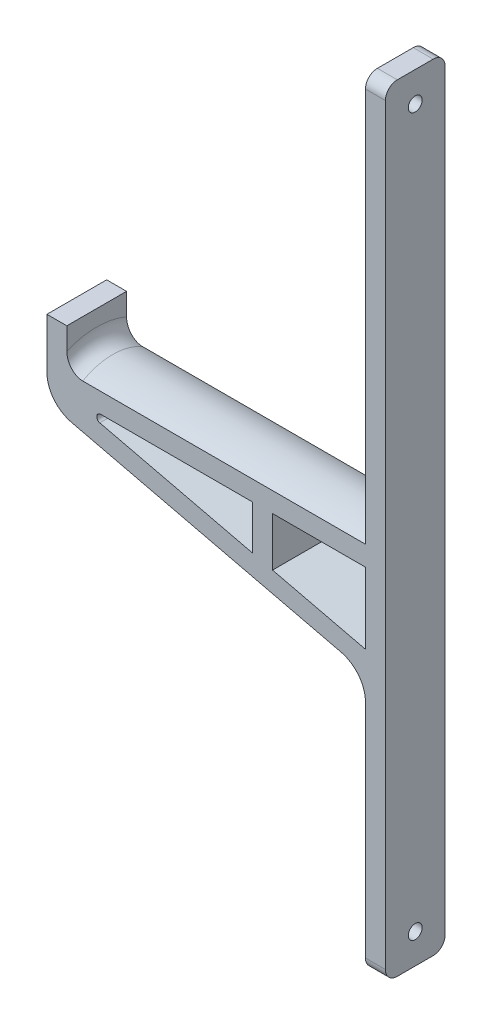
SolidWorks part; units mm, degrees
ref_plane "Plano frontal" through (0, 0, 0) normal (0, 0, 1) x (1, 0, 0)
ref_plane "Plano superior" through (0, 0, 0) normal (0, 1, 0) x (1, 0, 0)
ref_plane "Plano direito" through (0, 0, 0) normal (1, 0, 0) x (0, 0, -1)
sketch "Esboço1" plane through (0, 0, 0) normal (0, 0, 1) x (1, 0, 0)
  line L0 (-2.5, -2.5) -> (-77.5, -2.5)
  line L1 (2.5, 97.5) -> (-2.5, 97.5)
  line L2 (2.5, 97.5) -> (2.5, -97.5)
  line L3 (2.5, -97.5) -> (-2.5, -97.5)
  line L4 (-2.5, 97.5) -> (-2.5, -2.5)
  line L5 (2.5, 97.5) -> (-2.5, -97.5) construction
  line L6 (2.5, -97.5) -> (-2.5, 97.5) construction
  line L7 (-82.5, -2.5) -> (-82.5, -13.4491)
  line L8 (-82.5, -13.4491) -> (-2.5, -32.5)
  line L9 (-2.5, -9.5) -> (-25.8333, -9.5)
  line L11 (-77.5, -9.5) -> (-30.8333, -20.613)
  line L12 (-30.8333, -9.5) -> (-30.8333, -20.613)
  line L13 (-30.8333, -9.5) -> (-77.5, -9.5)
  line L14 (-25.8333, -9.5) -> (-25.8333, -21.8037)
  line L15 (-25.8333, -21.8037) -> (-2.5, -27.3602)
  line L16 (-2.5, -9.5) -> (-2.5, -27.3602)
  line L17 (-2.5, -32.5) -> (-2.5, -97.5)
  line L19 (-77.5, -9.5) -> (-82.5, -9.5) construction
  line L20 (-54.1667, -6.2308) -> (-30.8333, -6.2308) construction
  line L21 (-30.8333, -20.613) -> (-31.9916, -25.477) construction
  line L22 (-82.5, -2.5) -> (-82.5, 5.5)
  line L23 (-82.5, 5.5) -> (-77.5, 5.5)
  line L24 (-77.5, 5.5) -> (-77.5, -2.5)
  point P0 (0, 0)
  point P11 (0, 0)
  point P16 (-82.4644, -17.3865)
  point P20 (-76.3706, -9)
  point P22 (-54.1667, -9.5)
  point P27 (-31.5442, -32.7628)
  point P29 (-77.9904, -22.4362)
  point P30 (0, 0)
  dimension "D1" = 195
  dimension "D2" = 80
  dimension "D3" = 95
  dimension "D4" = 5
  dimension "D6" = 5
  dimension "D7" = 5
  dimension "D8" = 30
  dimension "D9" = 8
  dimension "D10" = 7
extrude "Ressalto-extrusão1" add sketch "Esboço1" along normal mid plane 15
sketch "Esboço2" plane through (-2.5, 0, 0) normal (-1, 0, 0) x (0, 0, 1)
  line L0 (-7.5, 0) -> (7.5, 0) construction
  line L1 (7.5, 97.5) -> (7.5, -2.5) construction
  line L2 (-7.5, 97.5) -> (-7.5, -2.5) construction
  circle A0 centre (0, 90) radius 1.75
  circle A1 centre (0, -90) radius 1.75
  point P9 (0, 0)
  point P10 (0, 0)
  point P11 (-7.5, 0)
  dimension "D2" = 3.5
  dimension "D1" = 180
extrude "Corte-extrusão1" cut sketch "Esboço2" against normal blind 10
fillet "Filete1" radius 1 1 edges at (-77.5, -9.5, 0)
sketch "Esboço3" plane through (-82.5, 0, 0) normal (-1, 0, 0) x (0, 0, 1)
  line L0 (7.5, -2.5) -> (-7.5, -2.5) construction
  line L1 (7.5, -2.5) -> (-7.5, -2.5)
  line L2 (-7.5, -2.5) -> (-7.5, -4.5096)
  line L3 (-7.5, 5.5) -> (-7.5, -13.4491) construction
  line L4 (7.5, -4.5096) -> (7.5, -2.5)
  arc A0 (-7.5, -4.5096) -> (7.5, -4.5096) centre (0, -17.5) cw
  point P7 (0, 0)
  line M2 (-7.5, 5.5) -> (-7.5, -13.4491)
  line M4 (7.5, -13.4491) -> (7.5, 5.5)
  dimension "D1" = 15
extrude "Corte-extrusão2" cut sketch "Esboço3" against normal up to vertex (80 mm away) from vertex at -5 contours L1 A0 M4 | A0 L1 M2 starting at point (-77.5, -2.5, 7.5)
fillet "Filete2" radius 3 4 edges at (0, -97.5, -7.5) (0, -97.5, 7.5) (0, 97.5, -7.5) (0, 97.5, 7.5)
fillet "Filete3" radius 8 2 edges at (-82.5, -13.4491, 0) (-2.5, -32.5, 0)
fillet "Filete4" radius 4 1 edges at (-77.5, -2.5, 0)
